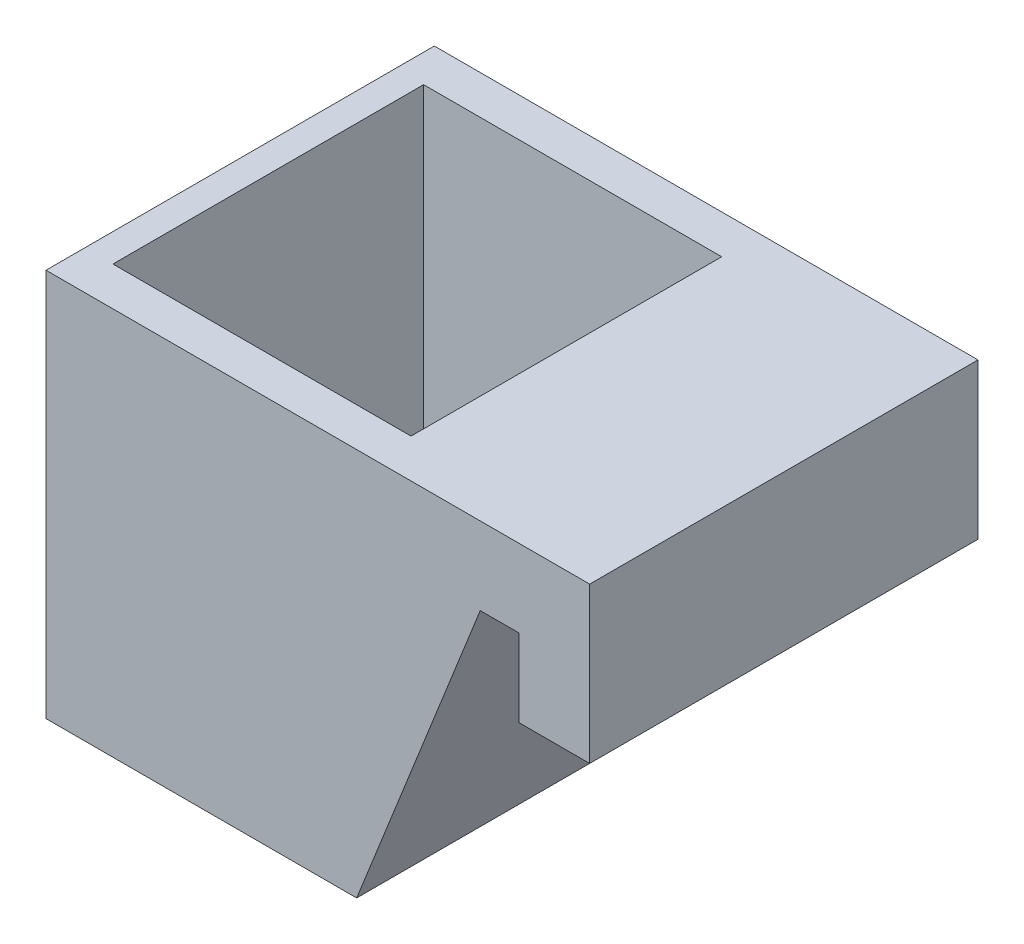
SolidWorks part; units mm, degrees
ref_plane "Front Plane" through (0, 0, 0) normal (0, 0, 1) x (1, 0, 0)
ref_plane "Top Plane" through (0, 0, 0) normal (0, 1, 0) x (1, 0, 0)
ref_plane "Right Plane" through (0, 0, 0) normal (1, 0, 0) x (0, 0, -1)
sketch "Sketch1" plane through (0, 0, 0) normal (0, 0, 1) x (1, 0, 0)
  line L0 (-55.9091, 31.8182) -> (-55.9091, -18.1818)
  line L1 (-55.9091, -18.1818) -> (-15.9091, -18.1818)
  line L2 (-15.9091, -18.1818) -> (0, 21.8182)
  line L3 (0, 21.8182) -> (5, 21.8182)
  line L4 (5, 21.8182) -> (5, 11.8182)
  line L5 (5, 11.8182) -> (14.0909, 11.8182)
  line L6 (14.0909, 11.8182) -> (14.0909, 31.8182)
  line L7 (14.0909, 31.8182) -> (-55.9091, 31.8182)
  dimension "D1" = 50
  dimension "D2" = 40
  dimension "D3" = 70
  dimension "D4" = 40
  dimension "D5" = 10
  dimension "D6" = 5
extrude "Boss-Extrude1" add sketch "Sketch1" along normal blind 50
sketch "Sketch2" plane through (0, 31.8182, 0) normal (0, 1, 0) x (1, 0, 0)
  line L0 (14.0909, 0) -> (-55.9091, 0) construction
  line L1 (-13.9091, -5) -> (-52.291, -5)
  line L2 (-13.9091, -5) -> (-13.9091, -45)
  line L3 (-13.9091, -45) -> (-52.291, -45)
  line L4 (-52.291, -5) -> (-52.291, -45)
  line L5 (14.0909, -50) -> (-55.9091, -50) construction
  line L6 (14.0909, -50) -> (14.0909, 0) construction
  dimension "D1" = 5
  dimension "D2" = 5
  dimension "D3" = 28
extrude "Cut-Extrude2" cut sketch "Sketch2" against normal blind 41
sketch "Sketch4" plane through (0, 0, 5) normal (0, 0, 1) x (1, 0, 0)
  line L1 (-38.3569, -3.5435) -> (-31.566, -3.5435)
  line L2 (-38.3569, -3.5435) -> (-38.3569, -7.3415)
  line L3 (-38.3569, -7.3415) -> (-31.566, -7.3415)
  line L4 (-31.566, -3.5435) -> (-31.566, -7.3415)
extrude "Cut-Extrude3" cut sketch "Sketch4" against normal blind 5
